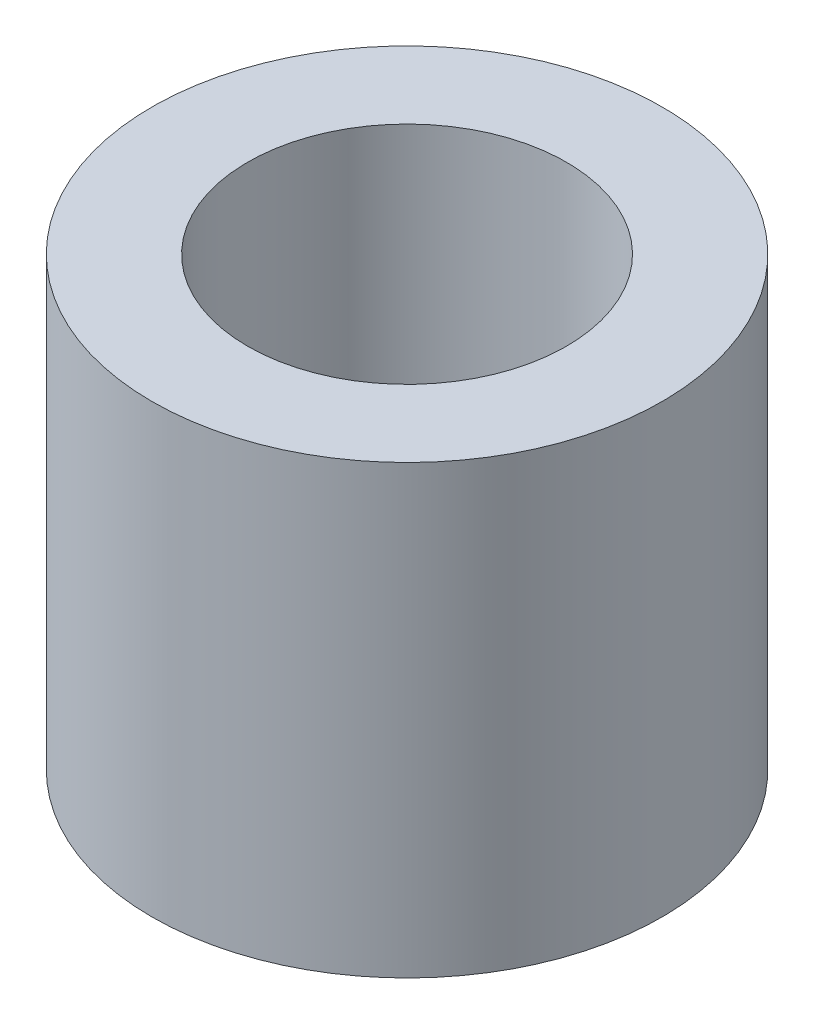
SolidWorks part; units mm, degrees
ref_plane "Front Plane" through (0, 0, 0) normal (0, 0, 1) x (1, 0, 0)
ref_plane "Top Plane" through (0, 0, 0) normal (0, 1, 0) x (1, 0, 0)
ref_plane "Right Plane" through (0, 0, 0) normal (1, 0, 0) x (0, 0, -1)
sketch "Sketch1" plane through (0, 0, 0) normal (0, 1, 0) x (1, 0, 0)
  circle A0 centre (0, 0) radius 2.5
  circle A1 centre (0, 0) radius 4
  dimension "D1" = 5
  dimension "D2" = 8
extrude "Boss-Extrude1" add sketch "Sketch1" along normal blind 7
